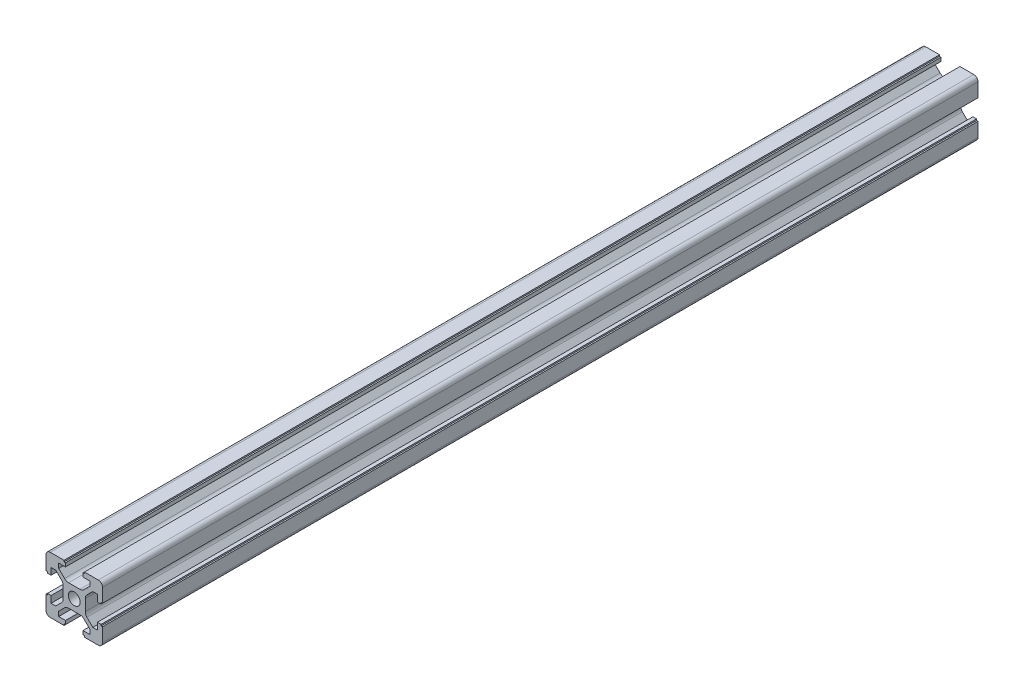
SolidWorks part; units mm, degrees
material "6061 合金"
ref_plane "前视基准面" through (0, 0, 0) normal (0, 0, 1) x (1, 0, 0)
ref_plane "上视基准面" through (0, 0, 0) normal (0, 1, 0) x (1, 0, 0)
ref_plane "右视基准面" through (0, 0, 0) normal (1, 0, 0) x (0, 0, -1)
sketch "草图1" plane through (0, 0, 0) normal (0, 0, 1) x (1, 0, 0)
  line L0 (-3.4251, 4.4858) -> (-5.5, 6.5607)
  line L6 (-5.5, 6.5607) -> (-5.5, 8.2)
  line L7 (-5.5, 8.2) -> (-3.1, 8.2)
  line L22 (-3.1, 8.2) -> (-3.1, 9.5)
  line L41 (-3.6, 10) -> (-8.5, 10)
  line L42 (0, 0) -> (-29.7212, 29.7212) construction
  line L43 (0, -8.5755) -> (0, 20.7623) construction
  line L44 (-10, 3.6) -> (-10, 8.5)
  line L46 (-8.2, 5.5) -> (-8.2, 3.1)
  line L47 (-6.5607, 5.5) -> (-8.2, 5.5)
  line L48 (-4.4858, 3.4251) -> (-6.5607, 5.5)
  line L49 (4.4858, 3.4251) -> (6.5607, 5.5)
  line L50 (6.5607, 5.5) -> (8.2, 5.5)
  line L51 (8.2, 5.5) -> (8.2, 3.1)
  line L53 (10, 3.6) -> (10, 8.5)
  line L54 (3.6, 10) -> (8.5, 10)
  line L56 (5.5, 8.2) -> (3.1, 8.2)
  line L57 (5.5, 6.5607) -> (5.5, 8.2)
  line L58 (3.4251, 4.4858) -> (5.5, 6.5607)
  line L59 (11, 0) -> (-11, 0) construction
  line L60 (3.4251, -4.4858) -> (5.5, -6.5607)
  line L61 (5.5, -6.5607) -> (5.5, -8.2)
  line L62 (5.5, -8.2) -> (3.1, -8.2)
  line L64 (3.6, -10) -> (8.5, -10)
  line L65 (10, -3.6) -> (10, -8.5)
  line L67 (8.2, -5.5) -> (8.2, -3.1)
  line L68 (6.5607, -5.5) -> (8.2, -5.5)
  line L69 (4.4858, -3.4251) -> (6.5607, -5.5)
  line L70 (-4.4858, -3.4251) -> (-6.5607, -5.5)
  line L71 (-6.5607, -5.5) -> (-8.2, -5.5)
  line L72 (-8.2, -5.5) -> (-8.2, -3.1)
  line L74 (-10, -3.6) -> (-10, -8.5)
  line L75 (-3.6, -10) -> (-8.5, -10)
  line L77 (-5.5, -8.2) -> (-3.1, -8.2)
  line L78 (-5.5, -6.5607) -> (-5.5, -8.2)
  line L79 (-3.4251, -4.4858) -> (-5.5, -6.5607)
  line L80 (-3.9, -2.0109) -> (-3.9, 2.0109)
  line L81 (-2.0109, 3.9) -> (2.0109, 3.9)
  line L82 (3.9, 2.0109) -> (3.9, -2.0109)
  line L83 (2.0109, -3.9) -> (-2.0109, -3.9)
  line L84 (-3.1, 9.5) -> (-3.6, 9.5)
  line L85 (-3.6, 9.5) -> (-3.6, 10)
  line L86 (3.6, 9.5) -> (3.6, 10)
  line L87 (3.1, 9.5) -> (3.6, 9.5)
  line L88 (3.1, 8.2) -> (3.1, 9.5)
  line L89 (-9.5, 3.1) -> (-9.5, 3.6)
  line L90 (-9.5, 3.6) -> (-10, 3.6)
  line L91 (-8.2, 3.1) -> (-9.5, 3.1)
  line L92 (8.2, 3.1) -> (9.5, 3.1)
  line L93 (9.5, 3.6) -> (10, 3.6)
  line L94 (9.5, 3.1) -> (9.5, 3.6)
  line L95 (9.5, -3.1) -> (9.5, -3.6)
  line L96 (9.5, -3.6) -> (10, -3.6)
  line L97 (8.2, -3.1) -> (9.5, -3.1)
  line L98 (3.1, -8.2) -> (3.1, -9.5)
  line L99 (3.1, -9.5) -> (3.6, -9.5)
  line L100 (3.6, -9.5) -> (3.6, -10)
  line L101 (-3.6, -9.5) -> (-3.6, -10)
  line L102 (-3.1, -9.5) -> (-3.6, -9.5)
  line L103 (-3.1, -8.2) -> (-3.1, -9.5)
  line L104 (-8.2, -3.1) -> (-9.5, -3.1)
  line L105 (-9.5, -3.6) -> (-10, -3.6)
  line L106 (-9.5, -3.1) -> (-9.5, -3.6)
  circle A0 centre (0, 0) radius 2.1
  arc A1 (-10, -8.5) -> (-8.5, -10) centre (-8.5, -8.5) ccw
  arc A2 (8.5, -10) -> (10, -8.5) centre (8.5, -8.5) ccw
  arc A3 (10, 8.5) -> (8.5, 10) centre (8.5, 8.5) ccw
  arc A4 (-8.5, 10) -> (-10, 8.5) centre (-8.5, 8.5) ccw
  arc A5 (-4.4858, 3.4251) -> (-3.9, 2.0109) centre (-5.9, 2.0109) cw
  arc A6 (-3.4251, 4.4858) -> (-2.0109, 3.9) centre (-2.0109, 5.9) ccw
  arc A7 (3.4251, 4.4858) -> (2.0109, 3.9) centre (2.0109, 5.9) cw
  arc A8 (4.4858, 3.4251) -> (3.9, 2.0109) centre (5.9, 2.0109) ccw
  arc A9 (4.4858, -3.4251) -> (3.9, -2.0109) centre (5.9, -2.0109) cw
  arc A10 (-4.4858, -3.4251) -> (-3.9, -2.0109) centre (-5.9, -2.0109) ccw
  arc A11 (3.4251, -4.4858) -> (2.0109, -3.9) centre (2.0109, -5.9) ccw
  arc A12 (-3.4251, -4.4858) -> (-2.0109, -3.9) centre (-2.0109, -5.9) cw
  point P74 (-10, -10)
  point P77 (10, -10)
  point P80 (10, 10)
  point P83 (-10, 10)
  point P86 (-3.9, 2.8393)
  point P89 (-2.8393, 3.9)
  point P92 (2.8393, 3.9)
  point P95 (3.9, 2.8393)
  point P98 (3.9, -2.8393)
  point P101 (-3.9, -2.8393)
  point P104 (2.8393, -3.9)
  point P107 (-2.8393, -3.9)
  dimension "D8" = 4.2
  dimension "D7" = 1.5
  dimension "D12" = 2
  dimension "D1" = 45
  dimension "D2" = 20
  dimension "D3" = 0.5
  dimension "D4" = 6.2
  dimension "D5" = 11
  dimension "D6" = 1.5
  dimension "D9" = 0.5
  dimension "D10" = 1.8
  dimension "D11" = 6.1
extrude "凸台-拉伸1" add sketch "草图1" along normal mid plane 310
